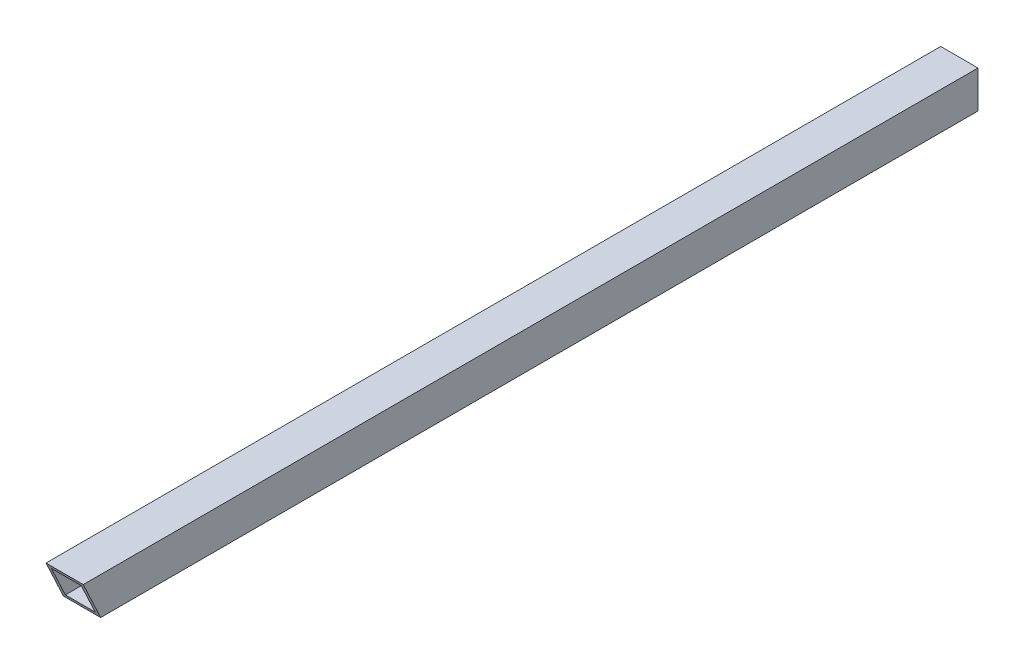
SolidWorks part; units mm, degrees
material "AISI 304"
ref_plane "Front Plane" through (0, 0, 0) normal (0, 0, 1) x (1, 0, 0)
ref_plane "Top Plane" through (0, 0, 0) normal (0, 1, 0) x (1, 0, 0)
ref_plane "Right Plane" through (0, 0, 0) normal (1, 0, 0) x (0, 0, -1)
sketch "Sketch4" plane through (0, 0, 0) normal (0, 0, 1) x (1, 0, 0)
  line L1 (9.525, -9.525) -> (-9.525, -9.525)
  line L2 (9.525, -9.525) -> (9.525, 9.525)
  line L3 (9.525, 9.525) -> (-9.525, 9.525)
  line L4 (-9.525, -9.525) -> (-9.525, 9.525)
  line L5 (9.525, -9.525) -> (-9.525, 9.525) construction
  line L6 (9.525, 9.525) -> (-9.525, -9.525) construction
  line L7 (7.62, -7.62) -> (-7.62, -7.62)
  line L8 (7.62, -7.62) -> (7.62, 7.62)
  line L9 (7.62, 7.62) -> (-7.62, 7.62)
  line L10 (-7.62, -7.62) -> (-7.62, 7.62)
  line L11 (7.62, -7.62) -> (-7.62, 7.62) construction
  line L12 (7.62, 7.62) -> (-7.62, -7.62) construction
  point P0 (0, 0)
  point P1 (0, 0)
  dimension "D1" = 15.24
  dimension "D2" = 19.05
extrude "Boss-Extrude2" add sketch "Sketch4" along normal blind 457.2
sketch "Sketch5" plane through (9.525, 0, 0) normal (1, 0, 0) x (0, 0, -1)
  line L0 (-457.2, 9.525) -> (-448.3168, -9.525)
  line L1 (-457.2, -9.525) -> (0, -9.525) construction
  line L2 (-448.3168, -9.525) -> (-457.2, -9.525)
  line L3 (-457.2, -9.525) -> (-457.2, 9.525)
  dimension "D1" = 25
extrude "Cut-Extrude1" cut sketch "Sketch5" against normal through all
sketch "Sketch6" plane through (0, -173.4165, 371.893) normal (0, -0.4226, 0.9063) x (1, 0, 0)
  line L0 (-9.525, 180.8343) -> (9.525, 180.8343) construction
  line L1 (-9.525, 201.8537) -> (9.525, 201.8537)
  line L2 (-9.525, 201.8537) -> (-9.525, 180.8343)
  line L3 (-9.525, 180.8343) -> (9.525, 180.8343)
  line L4 (9.525, 201.8537) -> (9.525, 180.8343)
  line L5 (9.525, 180.8343) -> (9.525, 201.8537) construction
  line L7 (-7.62, 199.7517) -> (7.62, 199.7517)
  line L8 (-7.62, 199.7517) -> (-7.62, 182.9362)
  line L9 (-7.62, 182.9362) -> (7.62, 182.9362)
  line L10 (7.62, 199.7517) -> (7.62, 182.9362)
sketch "Sketch7" plane through (0, 0, 0) normal (1, 0, 0) x (0, 0, -1)
  line L0 (-452.7584, 0) -> (-360.6775, 42.938) construction
  line L1 (-360.6775, 42.938) -> (0, 0) construction
  line L2 (-452.7584, 0) -> (0, 0) construction
  line L3 (-457.2, 9.525) -> (-448.3168, -9.525) construction
  point P2 (0, 0)
  point P7 (0, 0)
  point P8 (0, 0)
  dimension "D1" = 25
  dimension "D2" = 101.6
